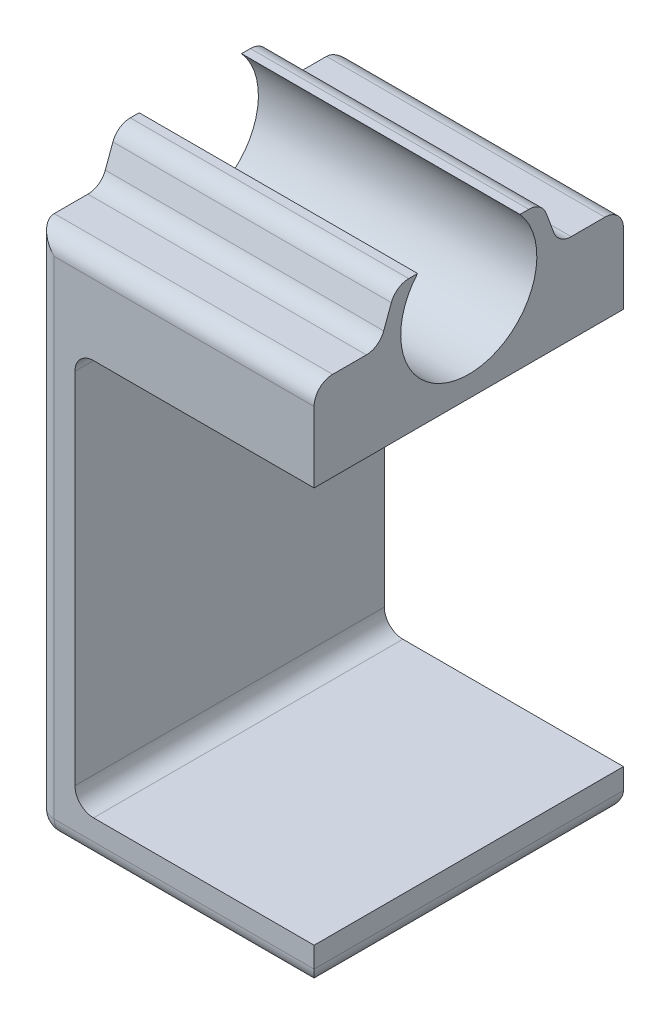
SolidWorks part; units mm, degrees
ref_plane "Front Plane" through (0, 0, 0) normal (0, 0, 1) x (1, 0, 0)
ref_plane "Top Plane" through (0, 0, 0) normal (0, 1, 0) x (1, 0, 0)
ref_plane "Right Plane" through (0, 0, 0) normal (1, 0, 0) x (0, 0, -1)
sketch "Sketch1" plane through (0, 0, 0) normal (0, 1, 0) x (1, 0, 0)
  line L1 (-22.5, -25) -> (22.5, -25)
  line L2 (-22.5, -25) -> (-22.5, 25)
  line L3 (-22.5, 25) -> (22.5, 25)
  line L4 (22.5, -25) -> (22.5, 25)
  line L5 (-22.5, -25) -> (22.5, 25) construction
  line L6 (-22.5, 25) -> (22.5, -25) construction
  point P0 (0, 0)
  dimension "D1" = 45
  dimension "D2" = 50
extrude "Boss-Extrude1" add sketch "Sketch1" along normal blind 92
sketch "Sketch2" plane through (0, 0, -25) normal (0, 0, -1) x (-1, 0, 0)
  line L0 (-22.5, 92) -> (-22.5, 0) construction
  line L1 (-22.5, 6.35) -> (16.15, 6.35)
  line L2 (-22.5, 6.35) -> (-22.5, 70.35)
  line L3 (-22.5, 70.35) -> (16.15, 70.35)
  line L4 (16.15, 6.35) -> (16.15, 70.35)
  line L5 (-22.5, 0) -> (22.5, 0) construction
  line L6 (22.5, 92) -> (22.5, 0) construction
  dimension "D1" = 6.35
  dimension "D2" = 6.35
  dimension "D3" = 64
extrude "Cut-Extrude1" cut sketch "Sketch2" against normal up to surface (50 mm away) up to face at (0, 46, 25)
sketch "Sketch3" plane through (22.5, 0, 0) normal (1, 0, 0) x (0, 0, -1)
  line L0 (0, 92) -> (0, 77.5) construction
  line L1 (-25, 92) -> (25, 92) construction
  circle A0 centre (0, 84.75) radius 11
  dimension "D1" = 22
  dimension "D2" = 7.25
extrude "Cut-Extrude2" cut sketch "Sketch3" against normal up to surface (45 mm away) up to face at (-22.5, 46, 0)
fillet "Fillet1" radius 3 2 edges at (-16.15, 6.35, 0) (-16.15, 70.35, 0)
sketch "Sketch4" plane through (22.5, 0, 0) normal (1, 0, 0) x (0, 0, -1)
  line L0 (11.793, 92) -> (14.47, 84.75)
  line L1 (25, 92) -> (25, 70.35) construction
  line L2 (25, 84.75) -> (-25, 84.75) construction
  line L3 (-25, 92) -> (-25, 70.35) construction
  line L4 (8.2727, 92) -> (25, 92) construction
  line L5 (14.47, 84.75) -> (25, 84.75)
  line L6 (25, 84.75) -> (25, 92)
  line L7 (25, 92) -> (11.793, 92)
  line L8 (0, 84.75) -> (0, 92) construction
  line L9 (-25, 84.75) -> (-25, 92)
  line L10 (-14.47, 84.75) -> (-25, 84.75)
  line L11 (-11.793, 92) -> (-14.47, 84.75)
  line L12 (-25, 92) -> (-11.793, 92)
extrude "Cut-Extrude3" cut sketch "Sketch4" against normal up to surface (45 mm away) up to face at (-22.5, 58.2917, 0)
fillet "Fillet5" radius 3 4 edges at (0, 84.75, 14.47) (0, 92, 11.793) (0, 84.75, -14.47) (0, 92, -11.793)
fillet "Fillet6" radius 3 8 edges at (22.5, 0, 0) (0, 0, -25) (0, 0, 25) (-22.5, 0, 0) (0, 84.75, -25) (0, 84.75, 25) (-22.5, 42.375, 25) (-22.5, 42.375, -25)
sketch "Sketch5" plane through (-22.5, 0, 0) normal (-1, 0, 0) x (0, 0, 1)
  line L0 (-19.5199, 8.015) -> (19.2476, 8.015) construction
  text T0 "OneChair V3"
extrude "Cut-Extrude4" cut sketch "Sketch5" against normal blind 1
sketch "Sketch15" plane through (-22.5, 0, 0) normal (-1, 0, 0) x (0, 0, 1)
  line L3 (10.2596, 32.0046) -> (9.9115, 31.8204)
  line L7 (10.2596, 30.9578) -> (10.2596, 30.6198)
  line L10 (12.867, 34.9608) -> (4.2649, 30.6858)
  line L11 (14.52, 34.2529) -> (10.2596, 32.0046)
  line L12 (10.2596, 32.0046) -> (9.9115, 31.8204)
  line L13 (9.9115, 31.8204) -> (-14.2582, 18.9772)
  line L14 (-11.8535, 18.0077) -> (-8.8687, 18.0077)
  line L15 (10.2596, 30.0222) -> (10.2596, 30.9578)
  line L16 (10.828, 30.7106) -> (10.828, 30.7064)
  spline S7 degree 3 poles (-15.2979, 21.0019) (-15.3375, 21.2141) (-15.3567, 21.4299) (-15.3849, 21.6442) knots 29 29 29 29 30 30 30 30
  spline S8 degree 3 poles (-15.1435, 20.3562) (-15.1984, 20.5822) (-15.2583, 20.7902) (-15.2979, 21.0019) knots 28 28 28 28 29 29 29 29
  spline S9 degree 3 poles (-10.0647, 23.0588) (-11.7426, 22.1659) (-13.4314, 21.2673) (-15.1435, 20.3562) knots 27 27 27 27 28 28 28 28
  spline S10 degree 3 poles (-10.1505, 23.6586) (-10.1362, 23.4613) (-10.0952, 23.2658) (-10.0647, 23.0588) knots 26 26 26 26 27 27 27 27
  spline S11 degree 3 poles (-10.0043, 24.7775) (-10.1119, 24.4127) (-10.1781, 24.0401) (-10.1505, 23.6586) knots 25 25 25 25 26 26 26 26
  spline S12 degree 3 poles (-9.1188, 27.7673) (-9.4119, 26.7701) (-9.7102, 25.7744) (-10.0043, 24.7775) knots 24 24 24 24 25 25 25 25
  spline S13 degree 3 poles (-8.585, 28.698) (-8.8238, 28.4241) (-9.0148, 28.1212) (-9.1188, 27.7673) knots 23 23 23 23 24 24 24 24
  spline S14 degree 3 poles (-6.5207, 30.0144) (-7.3559, 29.8102) (-8.0265, 29.3386) (-8.585, 28.698) knots 22 22 22 22 23 23 23 23
  spline S15 degree 3 poles (-5.8867, 30.0896) (-6.0986, 30.0862) (-6.3152, 30.0646) (-6.5207, 30.0144) knots 21 21 21 21 22 22 22 22
  spline S16 degree 3 poles (-3.9427, 30.0956) (-4.5907, 30.095) (-5.2388, 30.0998) (-5.8867, 30.0896) knots 20 20 20 20 21 21 21 21
  spline S17 degree 3 poles (0.0807, 30.0993) (-1.2605, 30.097) (-2.6016, 30.0969) (-3.9427, 30.0956) knots 19 19 19 19 20 20 20 20
  spline S18 degree 3 poles (2.8334, 30.103) (1.916, 30.114) (0.9983, 30.1009) (0.0807, 30.0993) knots 18 18 18 18 19 19 19 19
  spline S19 degree 3 poles (3.4965, 30.2699) (3.284, 30.1558) (3.0781, 30.1) (2.8334, 30.103) knots 17 17 17 17 18 18 18 18
  spline S28 degree 3 poles (-12.5035, 30.7783) (-11.8211, 31.7697) (-10.94, 32.5326) (-9.8566, 33.0581) knots 5 5 5 5 6 6 6 6
  spline S29 degree 3 poles (-13.5209, 28.6858) (-13.2999, 29.4445) (-12.9836, 30.15) (-12.5035, 30.7783) knots 4 4 4 4 5 5 5 5
  spline S30 degree 3 poles (-15.205, 22.9992) (-14.6499, 24.8966) (-14.074, 26.7879) (-13.5209, 28.6858) knots 3 3 3 3 4 4 4 4
  spline S31 degree 3 poles (-15.3675, 22.092) (-15.3147, 22.3949) (-15.2907, 22.706) (-15.205, 22.9992) knots 2 2 2 2 3 3 3 3
  spline S32 degree 3 poles (-15.3849, 22.0015) (-15.3791, 22.0317) (-15.3728, 22.0618) (-15.3675, 22.092) knots 1 1 1 1 2 2 2 2
  spline S33 degree 3 poles (-15.3849, 21.6442) (-15.3849, 21.7633) (-15.3849, 21.8824) (-15.3849, 22.0015) knots 0 0 0 0 1 1 1 1
  spline S35 degree 3 poles (9.9115, 31.8204) (1.8611, 27.5421) (-6.186, 23.2664) (-14.2582, 18.9772) knots 3 3 3 3 4 4 4 4
  spline S36 degree 3 poles (-14.2582, 18.9772) (-14.0985, 18.8485) (-13.9614, 18.7241) (-13.8109, 18.6198) knots 4 4 4 4 5 5 5 5
  spline S37 degree 3 poles (-13.8109, 18.6198) (-13.2728, 18.2448) (-12.6632, 18.08) (-12.0175, 18.0287) knots 5 5 5 5 6 6 6 6
  spline S38 degree 3 poles (-12.0175, 18.0287) (-11.9629, 18.0245) (-11.9082, 18.0144) (-11.8535, 18.0077) knots 6 6 6 6 7 7 7 7
  spline S39 degree 3 poles (-15.3849, 21.6442) (-15.3563, 21.4298) (-15.3378, 21.2137) (-15.2975, 21.0018) knots 9 9 9 9 10 10 10 10
  spline S40 degree 3 poles (-15.2975, 21.0018) (-15.258, 20.7899) (-15.1983, 20.5822) (-15.1436, 20.3561) knots 10 10 10 10 11 11 11 11
  spline S41 degree 3 poles (-15.1436, 20.3561) (-13.4317, 21.2675) (-11.7426, 22.1663) (-10.0643, 23.0584) knots 11 11 11 11 12 12 12 12
  spline S42 degree 3 poles (-10.0643, 23.0584) (-10.0954, 23.2661) (-10.1366, 23.4612) (-10.1501, 23.6588) knots 12 12 12 12 13 13 13 13
  spline S43 degree 3 poles (-10.1501, 23.6588) (-10.1778, 24.0405) (-10.1122, 24.4129) (-10.0046, 24.7779) knots 13 13 13 13 14 14 14 14
  spline S44 degree 3 poles (-10.0046, 24.7779) (-9.7103, 25.7742) (-9.4119, 26.7697) (-9.1184, 27.7669) knots 14 14 14 14 15 15 15 15
  spline S45 degree 3 poles (-9.1184, 27.7669) (-9.015, 28.1209) (-8.8241, 28.4244) (-8.5853, 28.6977) knots 15 15 15 15 16 16 16 16
  spline S46 degree 3 poles (-8.5853, 28.6977) (-8.0262, 29.3384) (-7.3561, 29.8101) (-6.5203, 30.0144) knots 16 16 16 16 17 17 17 17
  spline S47 degree 3 poles (-6.5203, 30.0144) (-6.3152, 30.0648) (-6.0982, 30.0859) (-5.8864, 30.0892) knots 17 17 17 17 18 18 18 18
  spline S48 degree 3 poles (-5.8864, 30.0892) (-5.2389, 30.1002) (-4.5907, 30.0951) (-3.9424, 30.096) knots 18 18 18 18 19 19 19 19
  spline S49 degree 3 poles (-3.9424, 30.096) (-2.6013, 30.0968) (-1.2602, 30.0968) (0.0808, 30.0993) knots 19 19 19 19 20 20 20 20
  spline S50 degree 3 poles (0.0808, 30.0993) (0.9982, 30.101) (1.9163, 30.1144) (2.8336, 30.1027) knots 20 20 20 20 21 21 21 21
  spline S51 degree 3 poles (2.8336, 30.1027) (3.0783, 30.1002) (3.2843, 30.1556) (3.4962, 30.27) knots 21 21 21 21 22 22 22 22
  spline S52 degree 3 poles (3.4962, 30.27) (3.7524, 30.4092) (4.0087, 30.5475) (4.2649, 30.6858) knots 22 22 22 22 23 23 23 23
  spline S62 degree 3 poles (-15.3675, 22.092) (-15.3728, 22.0618) (-15.3791, 22.0317) (-15.3849, 22.0015) knots 9 9 9 9 10 10 10 10
  spline S63 degree 3 poles (-15.205, 22.9992) (-15.2907, 22.706) (-15.3147, 22.3949) (-15.3675, 22.092) knots 8 8 8 8 9 9 9 9
  spline S64 degree 3 poles (-13.5209, 28.6858) (-14.074, 26.7879) (-14.6499, 24.8966) (-15.205, 22.9992) knots 7 7 7 7 8 8 8 8
  spline S65 degree 3 poles (-12.5035, 30.7783) (-12.9836, 30.15) (-13.2999, 29.4445) (-13.5209, 28.6858) knots 6 6 6 6 7 7 7 7
  spline S66 degree 3 poles (-9.8566, 33.0581) (-10.94, 32.5326) (-11.8211, 31.7697) (-12.5035, 30.7783) knots 5 5 5 5 6 6 6 6
  spline S69 degree 3 poles (-8.8687, 18.0077) (-8.8317, 18.0127) (-8.7939, 18.0212) (-8.7569, 18.0212) knots 2 2 2 2 3 3 3 3
  spline S70 degree 3 poles (-8.7569, 18.0212) (-7.4225, 18.0228) (-6.0881, 18.0237) (-4.7538, 18.0254) knots 3 3 3 3 4 4 4 4
  spline S71 degree 3 poles (-4.7538, 18.0254) (-3.3286, 18.027) (-1.9035, 18.0279) (-0.4783, 18.0304) knots 4 4 4 4 5 5 5 5
  spline S72 degree 3 poles (-0.4783, 18.0304) (0.4987, 18.0321) (1.4757, 18.0338) (2.4527, 18.0388) knots 5 5 5 5 6 6 6 6
  spline S73 degree 3 poles (2.4527, 18.0388) (2.9118, 18.0413) (3.344, 18.175) (3.7627, 18.3491) knots 6 6 6 6 7 7 7 7
  spline S74 degree 3 poles (3.7627, 18.3491) (5.2963, 18.9872) (6.5576, 19.9735) (7.5253, 21.3255) knots 7 7 7 7 8 8 8 8
  spline S75 degree 3 poles (7.5253, 21.3255) (7.9466, 21.9132) (8.1921, 22.5808) (8.393, 23.272) knots 8 8 8 8 9 9 9 9
  spline S76 degree 3 poles (8.393, 23.272) (8.7991, 24.6694) (9.2229, 26.0618) (9.6341, 27.4575) knots 9 9 9 9 10 10 10 10
  spline S77 degree 3 poles (9.6341, 27.4575) (9.8098, 28.052) (9.9788, 28.6472) (10.1352, 29.2467) knots 10 10 10 10 11 11 11 11
  spline S78 degree 3 poles (10.1352, 29.2467) (10.1924, 29.4653) (10.2066, 29.6949) (10.2403, 29.9202) knots 11 11 11 11 12 12 12 12
  spline S79 degree 3 poles (10.2403, 29.9202) (10.2453, 29.9505) (10.2529, 29.9799) (10.2596, 30.0102) knots 12 12 12 12 13 13 13 13
  spline S80 degree 3 poles (-3.0486, 22.1503) (-0.3135, 24.0615) (2.4216, 25.9735) (5.1845, 27.9048) knots 8 8 8 8 9 9 9 9
  spline S81 degree 3 poles (-3.0369, 22.1293) (-3.0411, 22.1361) (-3.0444, 22.1428) (-3.0486, 22.1503) knots 7 7 7 7 8 8 8 8
  spline S82 degree 3 poles (-2.9957, 22.1276) (-3.0091, 22.1276) (-3.0234, 22.1285) (-3.0369, 22.1293) knots 6 6 6 6 7 7 7 7
  spline S83 degree 3 poles (1.2899, 22.1361) (-0.1386, 22.1243) (-1.5671, 22.1293) (-2.9957, 22.1276) knots 5 5 5 5 6 6 6 6
  spline S84 degree 3 poles (3.2196, 22.8306) (2.6587, 22.3774) (2.0088, 22.1428) (1.2899, 22.1361) knots 4 4 4 4 5 5 5 5
  spline S85 degree 3 poles (4.057, 24.0926) (3.8897, 23.6016) (3.629, 23.161) (3.2196, 22.8306) knots 3 3 3 3 4 4 4 4
  spline S86 degree 3 poles (4.4757, 25.4572) (4.3395, 25.0015) (4.21, 24.5424) (4.057, 24.0926) knots 2 2 2 2 3 3 3 3
  spline S87 degree 3 poles (5.145, 27.7106) (4.9222, 26.9598) (4.7002, 26.2081) (4.4757, 25.4572) knots 1 1 1 1 2 2 2 2
  spline S88 degree 3 poles (5.1845, 27.9048) (5.1677, 27.8207) (5.1601, 27.7644) (5.145, 27.7106) knots 0 0 0 0 1 1 1 1
  spline S93 degree 3 poles (-9.8566, 33.0581) (-9.2168, 33.6509) (-5.7863, 34.9432) (-4.9354, 35.2913) knots 5 5 5 5 6 6 6 6
  spline S94 degree 3 poles (-4.9354, 35.2913) (-4.0778, 35.6427) (-3.1823, 35.9) (-2.3071, 36.2086) knots 6 6 6 6 7 7 7 7
  spline S95 degree 3 poles (-2.3071, 36.2086) (-2.1599, 36.2607) (-1.9985, 36.3372) (-1.8984, 36.4499) knots 7 7 7 7 8 8 8 8
  spline S96 degree 3 poles (-1.8984, 36.4499) (-0.4228, 38.1197) (1.0444, 39.7972) (2.5124, 41.4729) knots 8 8 8 8 9 9 9 9
  spline S97 degree 3 poles (2.5124, 41.4729) (2.5385, 41.5031) (2.5604, 41.5368) (2.5957, 41.5847) knots 9 9 9 9 10 10 10 10
  spline S98 degree 3 poles (2.5957, 41.5847) (2.5309, 41.6301) (2.4754, 41.6738) (2.4158, 41.7091) knots 10 10 10 10 11 11 11 11
  spline S99 degree 3 poles (2.4158, 41.7091) (1.659, 42.1607) (0.8989, 42.6063) (0.1489, 43.067) knots 11 11 11 11 12 12 12 12
  spline S100 degree 3 poles (0.1489, 43.067) (-0.0091, 43.1637) (-0.0983, 43.1419) (-0.2269, 43.025) knots 12 12 12 12 13 13 13 13
  spline S101 degree 3 poles (-0.2269, 43.025) (-1.2233, 42.1195) (-2.2255, 41.219) (-3.2294, 40.321) knots 13 13 13 13 14 14 14 14
  spline S102 degree 3 poles (-3.2294, 40.321) (-4.1745, 39.476) (-5.6005, 39.687) (-6.1949, 40.7548) knots 14 14 14 14 15 15 15 15
  spline S103 degree 3 poles (-6.1949, 40.7548) (-6.6128, 41.5057) (-6.4665, 42.5155) (-5.8216, 43.0881) knots 15 15 15 15 16 16 16 16
  spline S104 degree 3 poles (-5.8216, 43.0881) (-4.3637, 44.3837) (-2.8788, 45.65) (-1.4351, 46.9616) knots 16 16 16 16 17 17 17 17
  spline S105 degree 3 poles (-1.4351, 46.9616) (-0.9517, 47.4006) (0.117, 47.4703) (0.6484, 47.1441) knots 17 17 17 17 18 18 18 18
  spline S106 degree 3 poles (0.6484, 47.1441) (1.9474, 46.3462) (3.2759, 45.5953) (4.5918, 44.8252) knots 18 18 18 18 19 19 19 19
  spline S107 degree 3 poles (4.5918, 44.8252) (6.1615, 43.9079) (7.7187, 42.9653) (9.307, 42.0816) knots 19 19 19 19 20 20 20 20
  spline S108 degree 3 poles (9.307, 42.0816) (10.2016, 41.583) (10.3933, 40.6615) (10.3025, 39.9687) knots 20 20 20 20 21 21 21 21
  spline S109 degree 3 poles (10.3025, 39.9687) (10.2436, 39.5146) (10.0637, 39.1169) (9.7526, 38.7655) knots 21 21 21 21 22 22 22 22
  spline S110 degree 3 poles (9.7526, 38.7655) (8.6167, 37.4816) (7.495, 36.1851) (6.3692, 34.8936) knots 22 22 22 22 23 23 23 23
  spline S111 degree 3 poles (6.3692, 34.8936) (6.312, 34.828) (6.2582, 34.7591) (6.1657, 34.6464) knots 23 23 23 23 24 24 24 24
  spline S112 degree 3 poles (6.1657, 34.6464) (6.2927, 34.6321) (6.3675, 34.6119) (6.4407, 34.6161) knots 24 24 24 24 25 25 25 25
  spline S113 degree 3 poles (6.4407, 34.6161) (8.5191, 34.7271) (10.5976, 34.8322) (12.6752, 34.9566) knots 25 25 25 25 26 26 26 26
  spline S114 degree 3 poles (12.6752, 34.9566) (12.74, 34.9608) (12.8047, 34.9617) (12.867, 34.9608) knots 26 26 26 26 27 27 27 27
  spline S115 degree 3 poles (14.8496, 33.4566) (14.7857, 33.7627) (14.6738, 34.0301) (14.52, 34.2529) knots 0 0 0 0 1 1 1 1
  spline S116 degree 3 poles (-14.2582, 18.9772) (-14.0985, 18.8485) (-13.9614, 18.7241) (-13.8109, 18.6198) knots 4 4 4 4 5 5 5 5
  spline S117 degree 3 poles (-13.8109, 18.6198) (-13.2728, 18.2448) (-12.6632, 18.08) (-12.0175, 18.0287) knots 5 5 5 5 6 6 6 6
  spline S118 degree 3 poles (-12.0175, 18.0287) (-11.9629, 18.0245) (-11.9082, 18.0144) (-11.8535, 18.0077) knots 6 6 6 6 7 7 7 7
  spline S119 degree 3 poles (-8.8687, 18.0077) (-8.8317, 18.0127) (-8.7939, 18.0212) (-8.7569, 18.0212) knots 8 8 8 8 9 9 9 9
  spline S120 degree 3 poles (-8.7569, 18.0212) (-7.4225, 18.0228) (-6.0881, 18.0237) (-4.7538, 18.0254) knots 9 9 9 9 10 10 10 10
  spline S121 degree 3 poles (-4.7538, 18.0254) (-3.3286, 18.027) (-1.9035, 18.0279) (-0.4783, 18.0304) knots 10 10 10 10 11 11 11 11
  spline S122 degree 3 poles (-0.4783, 18.0304) (0.4987, 18.0321) (1.4757, 18.0338) (2.4527, 18.0388) knots 11 11 11 11 12 12 12 12
  spline S123 degree 3 poles (2.4527, 18.0388) (2.9118, 18.0413) (3.344, 18.175) (3.7627, 18.3491) knots 12 12 12 12 13 13 13 13
  spline S124 degree 3 poles (3.7627, 18.3491) (5.2963, 18.9872) (6.5576, 19.9735) (7.5253, 21.3255) knots 13 13 13 13 14 14 14 14
  spline S125 degree 3 poles (7.5253, 21.3255) (7.9466, 21.9132) (8.1921, 22.5808) (8.393, 23.272) knots 14 14 14 14 15 15 15 15
  spline S126 degree 3 poles (8.393, 23.272) (8.7991, 24.6694) (9.2229, 26.0618) (9.6341, 27.4575) knots 15 15 15 15 16 16 16 16
  spline S127 degree 3 poles (9.6341, 27.4575) (9.8098, 28.052) (9.9788, 28.6472) (10.1352, 29.2467) knots 16 16 16 16 17 17 17 17
  spline S128 degree 3 poles (10.1352, 29.2467) (10.1924, 29.4653) (10.2066, 29.6949) (10.2403, 29.9202) knots 17 17 17 17 18 18 18 18
  spline S129 degree 3 poles (10.2403, 29.9202) (10.2447, 29.9466) (10.251, 29.9722) (10.257, 29.9984) knots 18 18 18 18 19 19 19 19
  spline S130 degree 3 poles (10.257, 29.9984) (10.2587, 30.0062) (10.2596, 30.0142) (10.2596, 30.0222) knots 19 19 19 19 20 20 20 20
  spline S131 degree 3 poles (10.2596, 30.9578) (10.2596, 31.0378) (10.322, 31.1039) (10.4019, 31.1082) knots 21 21 21 21 22 22 22 22
  spline S132 degree 3 poles (10.4019, 31.1082) (10.4037, 31.1083) (10.4055, 31.1084) (10.4073, 31.1085) knots 22 22 22 22 23 23 23 23
  spline S133 degree 3 poles (10.4073, 31.1085) (10.6357, 31.1211) (10.828, 30.9394) (10.828, 30.7106) knots 23 23 23 23 24 24 24 24
  spline S134 degree 3 poles (10.828, 30.7064) (10.7683, 29.9169) (10.7078, 29.1282) (10.6481, 28.3387) knots 25 25 25 25 26 26 26 26
  spline S135 degree 3 poles (10.6481, 28.3387) (10.527, 26.7109) (10.416, 25.0822) (10.2798, 23.4561) knots 26 26 26 26 27 27 27 27
  spline S136 degree 3 poles (10.2798, 23.4561) (10.2277, 22.8331) (10.453, 22.3193) (10.8734, 21.9132) knots 27 27 27 27 28 28 28 28
  spline S137 degree 3 poles (10.8734, 21.9132) (11.8689, 20.9514) (13.6792, 21.4987) (13.9718, 22.8491) knots 28 28 28 28 29 29 29 29
  spline S138 degree 3 poles (13.9718, 22.8491) (14.0752, 23.3241) (14.0844, 23.8202) (14.1248, 24.307) knots 29 29 29 29 30 30 30 30
  spline S139 degree 3 poles (14.1248, 24.307) (14.2492, 25.7952) (14.3661, 27.2843) (14.488, 28.7725) knots 30 30 30 30 31 31 31 31
  spline S140 degree 3 poles (14.488, 28.7725) (14.6099, 30.2608) (14.7344, 31.749) (14.8563, 33.238) knots 31 31 31 31 32 32 32 32
  spline S141 degree 3 poles (14.8563, 33.238) (14.8622, 33.3103) (14.8639, 33.386) (14.8496, 33.4566) knots 32 32 32 32 33 33 33 33
  spline S142 degree 3 poles (4.057, 24.0926) (3.8897, 23.6016) (3.629, 23.161) (3.2196, 22.8306) knots 8 8 8 8 9 9 9 9
  spline S143 degree 3 poles (4.4757, 25.4572) (4.3395, 25.0015) (4.21, 24.5424) (4.057, 24.0926) knots 7 7 7 7 8 8 8 8
  spline S144 degree 3 poles (5.145, 27.7106) (4.9222, 26.9598) (4.7002, 26.2081) (4.4757, 25.4572) knots 6 6 6 6 7 7 7 7
  spline S145 degree 3 poles (5.1845, 27.9048) (5.1677, 27.8207) (5.1601, 27.7644) (5.145, 27.7106) knots 5 5 5 5 6 6 6 6
  spline S146 degree 3 poles (-3.0486, 22.1503) (-0.3135, 24.0615) (2.4216, 25.9735) (5.1845, 27.9048) knots 4 4 4 4 5 5 5 5
  spline S147 degree 3 poles (-3.0369, 22.1293) (-3.0411, 22.1361) (-3.0444, 22.1428) (-3.0486, 22.1503) knots 3 3 3 3 4 4 4 4
  spline S148 degree 3 poles (-2.9957, 22.1276) (-3.0091, 22.1276) (-3.0234, 22.1285) (-3.0369, 22.1293) knots 2 2 2 2 3 3 3 3
  spline S149 degree 3 poles (1.2899, 22.1361) (-0.1386, 22.1243) (-1.5671, 22.1293) (-2.9957, 22.1276) knots 1 1 1 1 2 2 2 2
  spline S150 degree 3 poles (3.2196, 22.8306) (2.6587, 22.3774) (2.0088, 22.1428) (1.2899, 22.1361) knots 0 0 0 0 1 1 1 1
  spline S158 degree 3 poles (7.5381, 45.8286) (7.5373, 47.5059) (9.0149, 48.9528) (10.725, 48.9493) knots 3 3 3 3 4 4 4 4
  spline S159 degree 3 poles (10.7155, 42.5606) (8.9098, 42.5606) (7.539, 43.9705) (7.5381, 45.8286) knots 2 2 2 2 3 3 3 3
  spline S160 degree 3 poles (13.8947, 45.7198) (13.8872, 44.0064) (12.4322, 42.5606) (10.7155, 42.5606) knots 1 1 1 1 2 2 2 2
  spline S161 degree 3 poles (10.725, 48.9493) (12.4988, 48.9457) (13.9025, 47.5155) (13.8947, 45.7198) knots 0 0 0 0 1 1 1 1
extrude "Cut-Extrude6" cut sketch "Sketch15" against normal blind 1 contours S114 S113 S112 S111 S110 S109 S108 S107 S106 S105 S104 S103 S102 S101 S100 S99 S98 S97 S96 S95 S94 S93 S28 S29 S30 S31 S32 S33 S39 S7 S40 S8 S9 S41 S10 S42 S11 S43 S44 S12 S13 S45 S46 S14 S15 S16 | S161 S158 S159 S160 | S140 S141 S115 L11 L3 S35 S36 S37 S38 L14 S69 S70 S71 S72 S73 S74 S75 S76 S77 S78 S79 S130 L15 L7 S131 S132 S133 L16 S134 S135 S136 S137 S138 S139 S80 S88 S87 S86 S85 S84 S83 S82 S81
